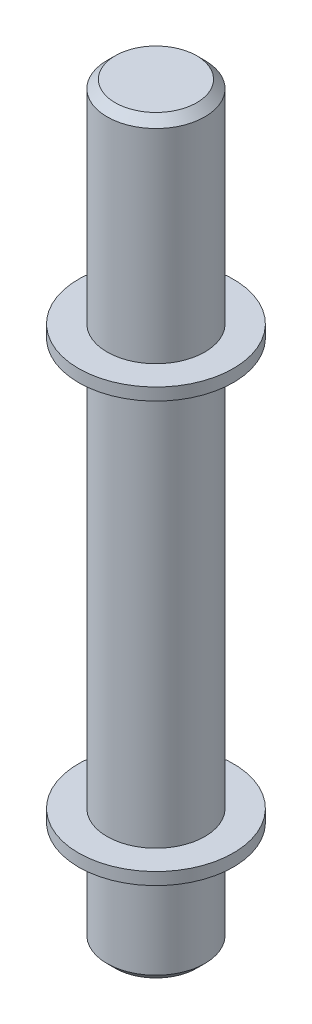
SolidWorks part; units mm, degrees
ref_plane "Front Plane" through (0, 0, 0) normal (0, 0, 1) x (1, 0, 0)
ref_plane "Top Plane" through (0, 0, 0) normal (0, 1, 0) x (1, 0, 0)
ref_plane "Right Plane" through (0, 0, 0) normal (1, 0, 0) x (0, 0, -1)
sketch "Sketch1" plane through (0, 0, 0) normal (1, 0, 0) x (0, 0, -1)
  line L0 (0, 0) -> (0, 228.1667) construction
  line L1 (0, 0) -> (12, 0)
  line L2 (12, 0) -> (12, 26)
  line L3 (12, 26) -> (19, 26)
  line L4 (19, 26) -> (19, 29)
  line L5 (19, 29) -> (12, 29)
  line L6 (12, 29) -> (12, 129)
  line L7 (12, 129) -> (19, 129)
  line L8 (19, 129) -> (19, 132)
  line L9 (19, 132) -> (12, 132)
  line L10 (12, 132) -> (12, 184)
  line L11 (12, 184) -> (0, 184)
  line L12 (0, 184) -> (0, 0)
  dimension "D1" = 12
  dimension "D2" = 26
  dimension "D3" = 3
  dimension "D4" = 100
  dimension "D5" = 3
  dimension "D6" = 52
  dimension "D7" = 12
  dimension "D8" = 12
  dimension "D9" = 19
  dimension "D10" = 12
  dimension "D11" = 19
revolve "Revolve1" add sketch "Sketch1" angle 360 about L12
chamfer "Chamfer3" distance 2 angle 45 2 edges at (0, 0, 12) (0, 184, 12)
cosmetic thread "Cosmetic Thread4" parameters "D1"=26, "D2"=20.704
cosmetic thread "Cosmetic Thread5" parameters "D1"=26, "D2"=20.704
